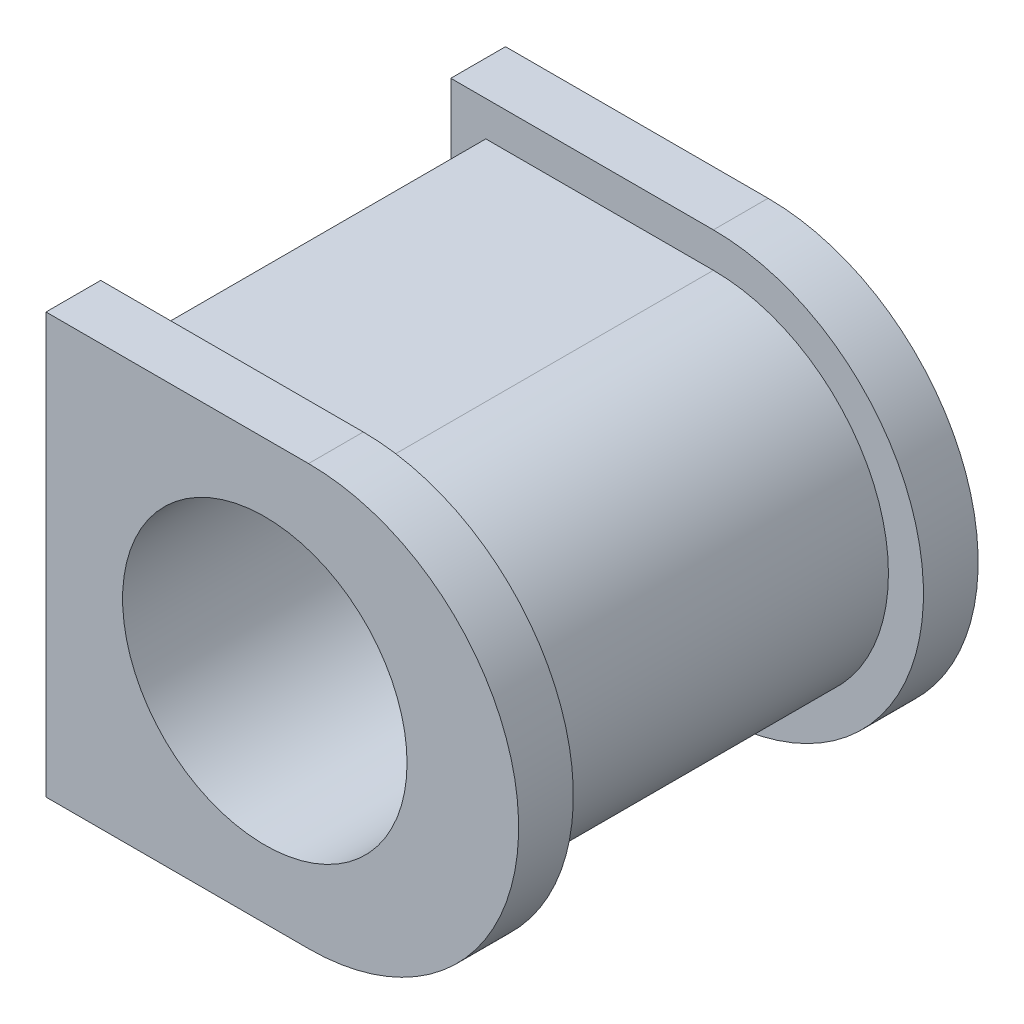
SolidWorks part; units mm, degrees
ref_plane "Front Plane" through (0, 0, 0) normal (0, 0, 1) x (1, 0, 0)
ref_plane "Top Plane" through (0, 0, 0) normal (0, 1, 0) x (1, 0, 0)
ref_plane "Right Plane" through (0, 0, 0) normal (1, 0, 0) x (0, 0, -1)
sketch "Sketch1" plane through (0, 0, 0) normal (0, 0, 1) x (1, 0, 0)
  line L0 (0, 48) -> (-60, 48)
  line L1 (-60, 48) -> (-60, -48)
  line L2 (-60, -48) -> (0, -48)
  arc A0 (0, -48) -> (0, 48) centre (0, 0) ccw
  dimension "D1" = 48
  dimension "D2" = 60
extrude "Boss-Extrude1" add sketch "Sketch1" along normal blind 12.5
sketch "Sketch2" plane through (0, 0, 12.5) normal (0, 0, 1) x (1, 0, 0)
  line L0 (0, 40) -> (-52, 40)
  line L1 (-52, 40) -> (-52, -40)
  line L2 (-52, -40) -> (0, -40)
  arc A0 (0, -40) -> (0, 40) centre (0, 0) ccw
  dimension "D1" = 80
  dimension "D2" = 52
extrude "Boss-Extrude2" add sketch "Sketch2" along normal blind 80
ref_plane "Plane1" through (0, 0, 52.5) normal (0, 0, 1) x (1, 0, 0)
mirror "Mirror1" about plane through (0, 0, 52.5) normal (0, 0, 1) of bodies 102
sketch "Sketch3" plane through (0, 0, 105) normal (0, 0, 1) x (1, 0, 0)
  line L0 (-10, 61.1837) -> (-10, -61.1837) construction
  line L1 (-77.1111, 0) -> (57.1111, 0) construction
  line L2 (-60, 48) -> (-60, -48) construction
  circle A0 centre (-10, 0) radius 32.5
  point P7 (-10, 0)
  point P8 (-10, 0)
  dimension "D2" = 65
  dimension "D1" = 50
extrude "Cut-Extrude1" cut sketch "Sketch3" against normal blind 120
